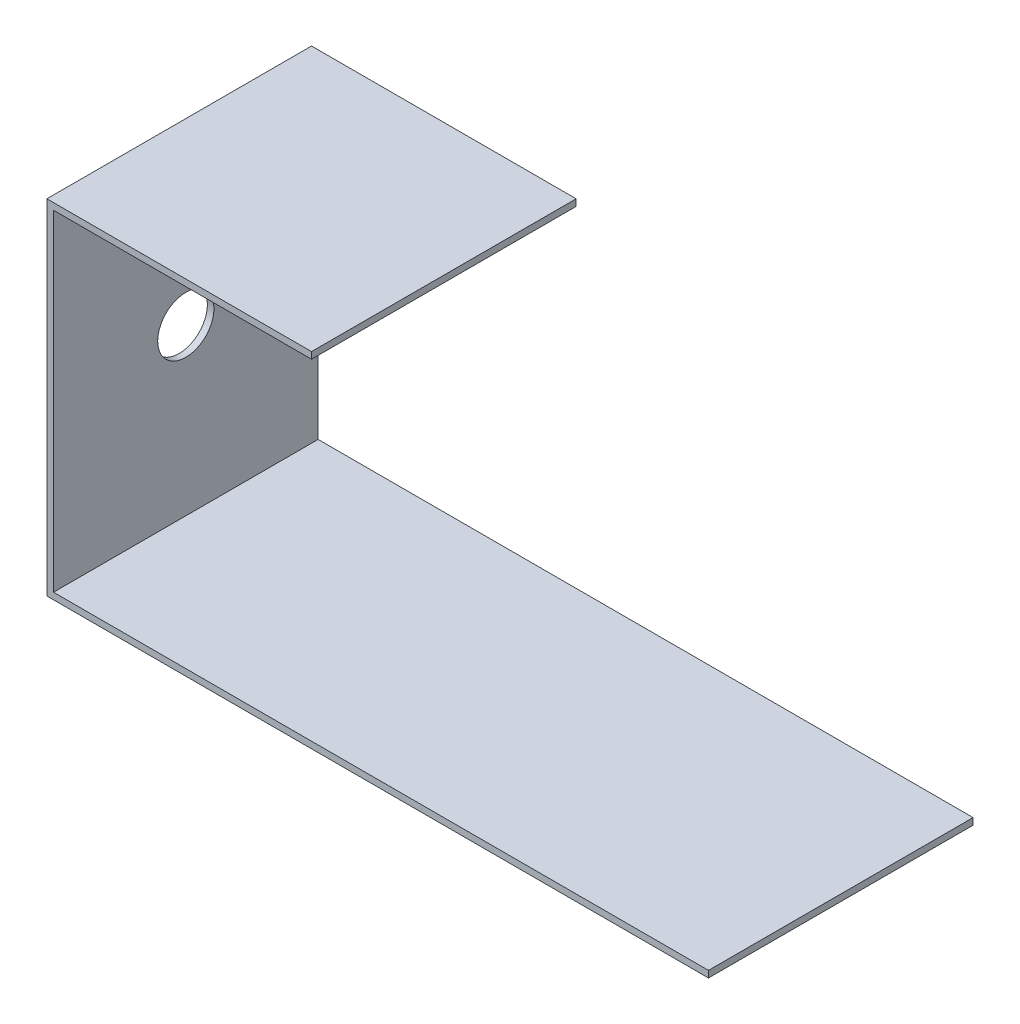
SolidWorks part; units mm, degrees
ref_plane "Front Plane" through (0, 0, 0) normal (0, 0, 1) x (1, 0, 0)
ref_plane "Top Plane" through (0, 0, 0) normal (0, 1, 0) x (1, 0, 0)
ref_plane "Right Plane" through (0, 0, 0) normal (1, 0, 0) x (0, 0, -1)
sketch "Sketch1" plane through (0, 0, 0) normal (0, 0, 1) x (1, 0, 0)
  line L0 (0, 0) -> (40, 0)
  line L1 (40, 0) -> (40, -1)
  line L2 (40, -1) -> (1, -1)
  line L3 (1, -1) -> (1, -51)
  line L4 (1, -51) -> (100, -51)
  line L5 (100, -51) -> (100, -52)
  line L6 (100, -52) -> (0, -52)
  line L7 (0, -52) -> (0, 0)
  dimension "D1" = 1
  dimension "D2" = 40
  dimension "D3" = 1
  dimension "D4" = 1
  dimension "D5" = 100
  dimension "D6" = 50
extrude "Boss-Extrude1" add sketch "Sketch1" along normal blind 40
sketch "Sketch2" plane through (0, 0, 0) normal (-1, 0, 0) x (0, 0, 1)
  line L0 (40, -26) -> (0, -26) construction
  line L1 (40, 0) -> (40, -52) construction
  line L2 (0, 0) -> (0, -52) construction
  line L3 (20, 0) -> (20, -52) construction
  line L4 (40, 0) -> (0, 0) construction
  line L5 (40, -52) -> (0, -52) construction
  circle A0 centre (20, -26) radius 4.25
  dimension "D1" = 8.5
extrude "Cut-Extrude1" cut sketch "Sketch2" against normal blind 1
